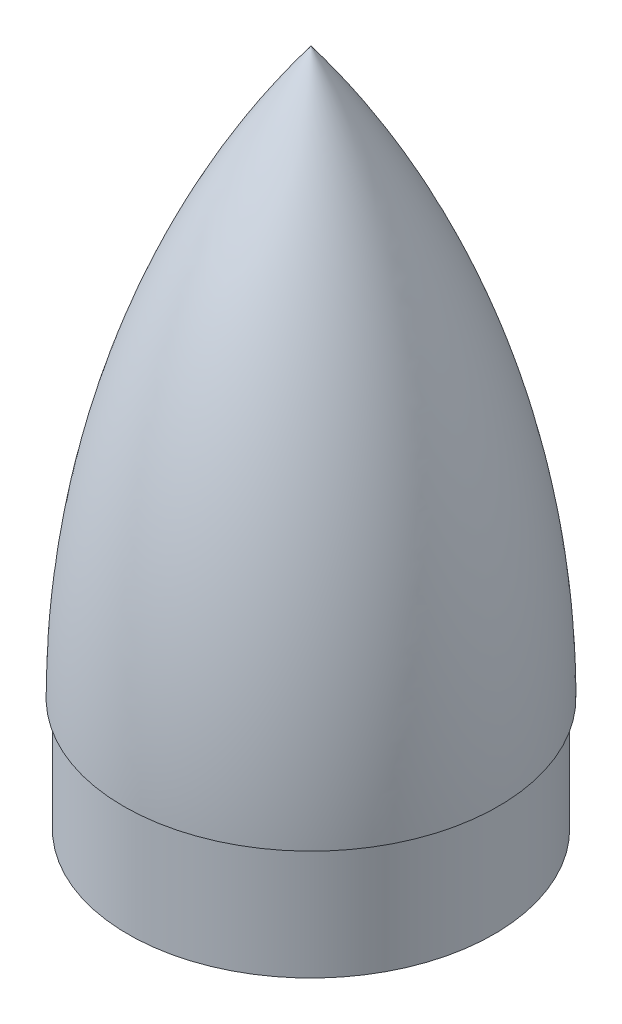
SolidWorks part; units mm, degrees
ref_plane "Front Plane" through (0, 0, 0) normal (0, 0, 1) x (1, 0, 0)
ref_plane "Top Plane" through (0, 0, 0) normal (0, 1, 0) x (1, 0, 0)
ref_plane "Right Plane" through (0, 0, 0) normal (1, 0, 0) x (0, 0, -1)
sketch "Sketch1" plane through (0, 0, 0) normal (0, 0, 1) x (1, 0, 0)
  line L2 (32.385, -20) -> (32.385, 0)
  line L3 (32.385, 0) -> (33.16, 0)
  line L4 (27.385, -20) -> (27.385, 7.8298)
  line L5 (32.385, -20) -> (27.385, -20)
  line L6 (0, 85) -> (0, 100)
  line L7 (26.5421, 24.1638) -> (22.799, 42.8866) construction
  line L8 (35.8939, 2.8907) -> (28.2882, 40.9346) construction
  line L9 (25.0095, 31.8299) -> (29.9124, 32.8101) construction
  arc A0 (0, 100) -> (33.16, 0) centre (-134.2041, 0) cw
  arc A1 (27.385, 7.8298) -> (0, 85) centre (-95.0392, 7.8298) ccw
  dimension "D1" = 100
  dimension "D2" = 5
  dimension "D3" = 20
  dimension "D4" = 32.385
  dimension "D5" = 33.16
  dimension "D6" = 15
  dimension "D7" = 5
revolve "Revolve1" add sketch "Sketch1" angle 360 about L6
